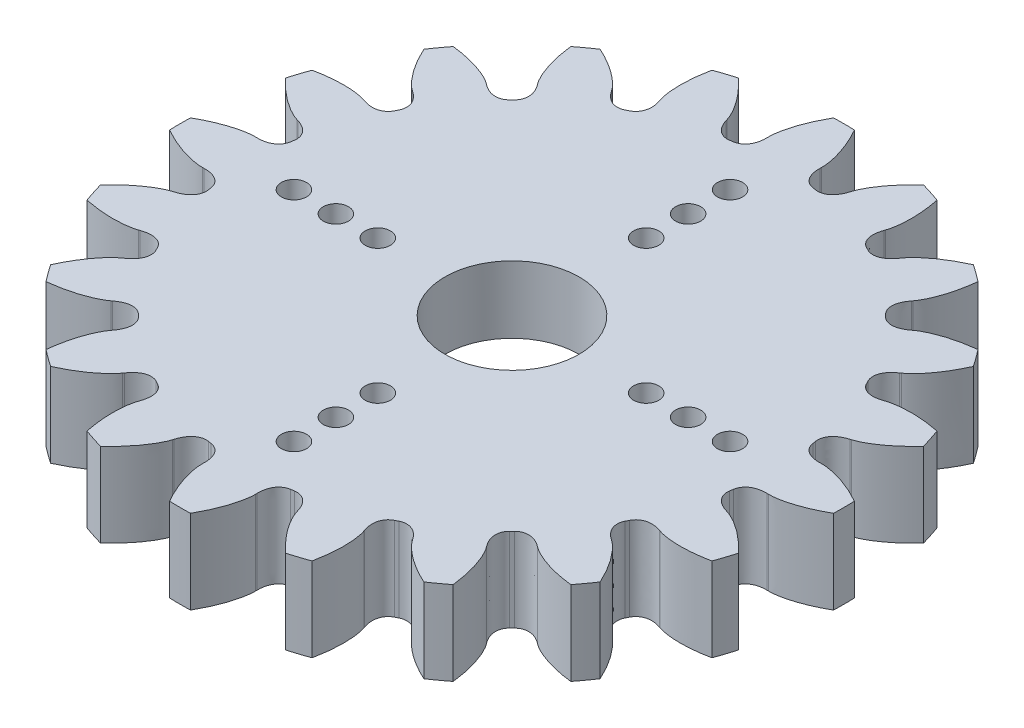
SolidWorks part; units mm, degrees
ref_plane "Front Plane" through (0, 0, 0) normal (0, 0, 1) x (1, 0, 0)
ref_plane "Top Plane" through (0, 0, 0) normal (0, 1, 0) x (1, 0, 0)
ref_plane "Right Plane" through (0, 0, 0) normal (1, 0, 0) x (0, 0, -1)
sketch "Sketch7" plane through (0, 0, 0) normal (0, 1, 0) x (1, 0, 0)
  line L80 (-16.4577, -3.6874) -> (-16.527, -3.709)
  line L81 (-16.8642, -1.5796) -> (-16.7917, -1.5788)
  line L82 (-16.7917, 1.5788) -> (-16.8642, 1.5796)
  line L83 (-16.527, 3.709) -> (-16.4577, 3.6874)
  line L84 (-15.482, 6.6904) -> (-15.5507, 6.7137)
  line L85 (-14.5719, 8.6346) -> (-14.5128, 8.5927)
  line L86 (-12.6568, 11.1472) -> (-12.715, 11.1905)
  line L87 (-11.1905, 12.715) -> (-11.1472, 12.6568)
  line L88 (-8.5927, 14.5128) -> (-8.6346, 14.5719)
  line L89 (-6.7137, 15.5507) -> (-6.6904, 15.482)
  line L90 (-3.6874, 16.4577) -> (-3.709, 16.527)
  line L91 (-1.5796, 16.8642) -> (-1.5788, 16.7917)
  line L92 (1.5788, 16.7917) -> (1.5796, 16.8642)
  line L93 (3.709, 16.527) -> (3.6874, 16.4577)
  line L94 (6.6904, 15.482) -> (6.7137, 15.5507)
  line L95 (8.6346, 14.5719) -> (8.5927, 14.5128)
  line L96 (11.1472, 12.6568) -> (11.1905, 12.715)
  line L97 (12.715, 11.1905) -> (12.6568, 11.1472)
  line L98 (14.5128, 8.5927) -> (14.5719, 8.6346)
  line L99 (15.5507, 6.7137) -> (15.482, 6.6904)
  line L100 (16.4577, 3.6874) -> (16.527, 3.709)
  line L101 (16.8642, 1.5796) -> (16.7917, 1.5788)
  line L102 (16.7917, -1.5788) -> (16.8642, -1.5796)
  line L103 (16.527, -3.709) -> (16.4577, -3.6874)
  line L104 (15.482, -6.6904) -> (15.5507, -6.7137)
  line L105 (14.5719, -8.6346) -> (14.5128, -8.5927)
  line L106 (12.6568, -11.1472) -> (12.715, -11.1905)
  line L107 (11.1905, -12.715) -> (11.1472, -12.6568)
  line L108 (8.5927, -14.5128) -> (8.6346, -14.5719)
  line L109 (6.7137, -15.5507) -> (6.6904, -15.482)
  line L110 (3.6874, -16.4577) -> (3.709, -16.527)
  line L111 (1.5796, -16.8642) -> (1.5788, -16.7917)
  line L112 (-1.5788, -16.7917) -> (-1.5796, -16.8642)
  line L113 (-3.709, -16.527) -> (-3.6874, -16.4577)
  line L114 (-6.6904, -15.482) -> (-6.7137, -15.5507)
  line L115 (-8.6346, -14.5719) -> (-8.5927, -14.5128)
  line L116 (-11.1472, -12.6568) -> (-11.1905, -12.715)
  line L117 (-12.715, -11.1905) -> (-12.6568, -11.1472)
  line L118 (-14.5128, -8.5927) -> (-14.5719, -8.6346)
  line L119 (-15.5507, -6.7137) -> (-15.482, -6.6904)
  arc A80 (-19.0148, -5.5208) -> (-18.6283, -6.7102) centre (0, 0) ccw
  arc A81 (-15.5716, -2.3637) -> (-15.5399, -2.5639) centre (0, 0) ccw
  arc A82 (-19.7901, 0.6253) -> (-19.7901, -0.6253) centre (0, 0) ccw
  arc A83 (-15.5399, 2.5639) -> (-15.5716, 2.3637) centre (0, 0) ccw
  arc A84 (-18.6283, 6.7102) -> (-19.0148, 5.5208) centre (0, 0) ccw
  arc A85 (-13.987, 7.2405) -> (-14.0791, 7.0599) centre (0, 0) ccw
  arc A86 (-15.643, 12.1382) -> (-16.3781, 11.1265) centre (0, 0) ccw
  arc A87 (-11.065, 11.2084) -> (-11.2084, 11.065) centre (0, 0) ccw
  arc A88 (-11.1265, 16.3781) -> (-12.1382, 15.643) centre (0, 0) ccw
  arc A89 (-7.0599, 14.0791) -> (-7.2405, 13.987) centre (0, 0) ccw
  arc A90 (-5.5208, 19.0148) -> (-6.7102, 18.6283) centre (0, 0) ccw
  arc A91 (-2.3637, 15.5716) -> (-2.5639, 15.5399) centre (0, 0) ccw
  arc A92 (0.6253, 19.7901) -> (-0.6253, 19.7901) centre (0, 0) ccw
  arc A93 (2.5639, 15.5399) -> (2.3637, 15.5716) centre (0, 0) ccw
  arc A94 (6.7102, 18.6283) -> (5.5208, 19.0148) centre (0, 0) ccw
  arc A95 (7.2405, 13.987) -> (7.0599, 14.0791) centre (0, 0) ccw
  arc A96 (12.1382, 15.643) -> (11.1265, 16.3781) centre (0, 0) ccw
  arc A97 (11.2084, 11.065) -> (11.065, 11.2084) centre (0, 0) ccw
  arc A98 (16.3781, 11.1265) -> (15.643, 12.1382) centre (0, 0) ccw
  arc A99 (14.0791, 7.0599) -> (13.987, 7.2405) centre (0, 0) ccw
  arc A100 (19.0148, 5.5208) -> (18.6283, 6.7102) centre (0, 0) ccw
  arc A101 (15.5716, 2.3637) -> (15.5399, 2.5639) centre (0, 0) ccw
  arc A102 (19.7901, -0.6253) -> (19.7901, 0.6253) centre (0, 0) ccw
  arc A103 (15.5399, -2.5639) -> (15.5716, -2.3637) centre (0, 0) ccw
  arc A104 (18.6283, -6.7102) -> (19.0148, -5.5208) centre (0, 0) ccw
  arc A105 (13.987, -7.2405) -> (14.0791, -7.0599) centre (0, 0) ccw
  arc A106 (15.643, -12.1382) -> (16.3781, -11.1265) centre (0, 0) ccw
  arc A107 (11.065, -11.2084) -> (11.2084, -11.065) centre (0, 0) ccw
  arc A108 (11.1265, -16.3781) -> (12.1382, -15.643) centre (0, 0) ccw
  arc A109 (7.0599, -14.0791) -> (7.2405, -13.987) centre (0, 0) ccw
  arc A110 (5.5208, -19.0148) -> (6.7102, -18.6283) centre (0, 0) ccw
  arc A111 (2.3637, -15.5716) -> (2.5639, -15.5399) centre (0, 0) ccw
  arc A112 (-0.6253, -19.7901) -> (0.6253, -19.7901) centre (0, 0) ccw
  arc A113 (-2.5639, -15.5399) -> (-2.3637, -15.5716) centre (0, 0) ccw
  arc A114 (-6.7102, -18.6283) -> (-5.5208, -19.0148) centre (0, 0) ccw
  arc A115 (-7.2405, -13.987) -> (-7.0599, -14.0791) centre (0, 0) ccw
  arc A116 (-12.1382, -15.643) -> (-11.1265, -16.3781) centre (0, 0) ccw
  arc A117 (-11.2084, -11.065) -> (-11.065, -11.2084) centre (0, 0) ccw
  arc A118 (-16.3781, -11.1265) -> (-15.643, -12.1382) centre (0, 0) ccw
  arc A119 (-14.0791, -7.0599) -> (-13.987, -7.2405) centre (0, 0) ccw
  spline S160 degree 3 poles (-16.527, -3.709) (-16.6119, -3.7336) (-16.7702, -3.7944) (-17.0187, -3.9123) (-17.2955, -4.0665) (-17.6234, -4.2783) (-17.9959, -4.555) (-18.4056, -4.9033) (-18.7477, -5.2353) (-18.9515, -5.4518) (-19.0148, -5.5208) knots 0 0 0 0 0.062091 0.118994 0.193136 0.284517 0.393136 0.518994 0.662091 0.72786 0.72786 0.72786 0.72786
  spline S161 degree 3 poles (-15.5399, -2.5639) (-15.5144, -2.7139) (-15.5425, -2.9348) (-15.672, -3.1736) (-15.7793, -3.3046) (-15.8929, -3.4073) (-16.0101, -3.4901) (-16.1313, -3.559) (-16.2793, -3.6275) (-16.3894, -3.6679) (-16.4577, -3.6874) knots 0 0 0 0 0.285204 0.404285 0.508742 0.603331 0.692375 0.779135 0.865928 1 1 1 1
  spline S162 degree 3 poles (-16.7917, -1.5788) (-16.7207, -1.5762) (-16.6035, -1.5807) (-16.4415, -1.6) (-16.305, -1.6281) (-16.1679, -1.6707) (-16.0282, -1.7332) (-15.8857, -1.8247) (-15.6887, -2.0117) (-15.5937, -2.2131) (-15.5716, -2.3637) knots 0 0 0 0 0.134072 0.220865 0.307625 0.396669 0.491258 0.595715 0.714796 1 1 1 1
  spline S163 degree 3 poles (-19.7901, -0.6253) (-19.7087, -0.6714) (-19.4479, -0.8143) (-19.02, -1.0243) (-18.5227, -1.2289) (-18.0829, -1.3771) (-17.7056, -1.4771) (-17.3947, -1.5383) (-17.122, -1.5736) (-16.9526, -1.5825) (-16.8642, -1.5796) knots 0.27214 0.27214 0.27214 0.27214 0.337909 0.481006 0.606864 0.715483 0.806864 0.881006 0.937909 1 1 1 1
  spline S164 degree 3 poles (-16.8642, 1.5796) (-16.9526, 1.5825) (-17.122, 1.5736) (-17.3947, 1.5383) (-17.7056, 1.4771) (-18.0829, 1.3771) (-18.5227, 1.2289) (-19.02, 1.0243) (-19.4479, 0.8143) (-19.7087, 0.6714) (-19.7901, 0.6253) knots 0 0 0 0 0.062091 0.118994 0.193136 0.284517 0.393136 0.518994 0.662091 0.72786 0.72786 0.72786 0.72786
  spline S165 degree 3 poles (-15.5716, 2.3637) (-15.5937, 2.2131) (-15.6887, 2.0117) (-15.8857, 1.8247) (-16.0282, 1.7332) (-16.1679, 1.6707) (-16.305, 1.6281) (-16.4415, 1.6) (-16.6035, 1.5807) (-16.7207, 1.5762) (-16.7917, 1.5788) knots 0 0 0 0 0.285204 0.404285 0.508742 0.603331 0.692375 0.779135 0.865928 1 1 1 1
  spline S166 degree 3 poles (-16.4577, 3.6874) (-16.3894, 3.6679) (-16.2793, 3.6275) (-16.1313, 3.559) (-16.0101, 3.4901) (-15.8929, 3.4073) (-15.7793, 3.3046) (-15.672, 3.1736) (-15.5425, 2.9348) (-15.5144, 2.7139) (-15.5399, 2.5639) knots 0 0 0 0 0.134072 0.220865 0.307625 0.396669 0.491258 0.595715 0.714796 1 1 1 1
  spline S167 degree 3 poles (-19.0148, 5.5208) (-18.9515, 5.4518) (-18.7477, 5.2353) (-18.4056, 4.9033) (-17.9959, 4.555) (-17.6234, 4.2783) (-17.2955, 4.0665) (-17.0187, 3.9123) (-16.7702, 3.7944) (-16.6119, 3.7336) (-16.527, 3.709) knots 0.27214 0.27214 0.27214 0.27214 0.337909 0.481006 0.606864 0.715483 0.806864 0.881006 0.937909 1 1 1 1
  spline S168 degree 3 poles (-15.5507, 6.7137) (-15.6339, 6.7437) (-15.7977, 6.7875) (-16.068, 6.8383) (-16.3825, 6.8762) (-16.7723, 6.8976) (-17.2364, 6.8926) (-17.7725, 6.8517) (-18.2445, 6.7842) (-18.5366, 6.7289) (-18.6283, 6.7102) knots 0 0 0 0 0.062091 0.118994 0.193136 0.284517 0.393136 0.518994 0.662091 0.72786 0.72786 0.72786 0.72786
  spline S169 degree 3 poles (-14.0791, 7.0599) (-14.1466, 6.9235) (-14.2992, 6.7613) (-14.5443, 6.6443) (-14.7081, 6.6014) (-14.8604, 6.5851) (-15.0039, 6.587) (-15.1424, 6.6024) (-15.3024, 6.6341) (-15.4152, 6.6661) (-15.482, 6.6904) knots 0 0 0 0 0.285204 0.404285 0.508742 0.603331 0.692375 0.779135 0.865928 1 1 1 1
  spline S170 degree 3 poles (-14.5128, 8.5927) (-14.4538, 8.553) (-14.3616, 8.4805) (-14.2419, 8.3697) (-14.148, 8.2667) (-14.0621, 8.1517) (-13.9858, 8.0189) (-13.9243, 7.8611) (-13.8749, 7.5941) (-13.9164, 7.3753) (-13.987, 7.2405) knots 0 0 0 0 0.134072 0.220865 0.307625 0.396669 0.491258 0.595715 0.714796 1 1 1 1
  spline S171 degree 3 poles (-16.3781, 11.1265) (-16.3393, 11.0413) (-16.2123, 10.7724) (-15.9896, 10.351) (-15.7076, 9.8931) (-15.4388, 9.5148) (-15.1923, 9.212) (-14.9768, 8.9799) (-14.7769, 8.791) (-14.6451, 8.6843) (-14.5719, 8.6346) knots 0.27214 0.27214 0.27214 0.27214 0.337909 0.481006 0.606864 0.715483 0.806864 0.881006 0.937909 1 1 1 1
  spline S172 degree 3 poles (-12.715, 11.1905) (-12.7848, 11.2447) (-12.9271, 11.3371) (-13.1685, 11.4689) (-13.4559, 11.6021) (-13.82, 11.7429) (-14.2628, 11.8816) (-14.7854, 12.0083) (-15.2551, 12.09) (-15.55, 12.1276) (-15.643, 12.1382) knots 0 0 0 0 0.062091 0.118994 0.193136 0.284517 0.393136 0.518994 0.662091 0.72786 0.72786 0.72786 0.72786
  spline S173 degree 3 poles (-11.2084, 11.065) (-11.3147, 10.9562) (-11.51, 10.8491) (-11.7792, 10.8136) (-11.9483, 10.8233) (-12.0981, 10.8549) (-12.2341, 10.901) (-12.361, 10.9585) (-12.5034, 11.0381) (-12.6008, 11.1034) (-12.6568, 11.1472) knots 0 0 0 0 0.285204 0.404285 0.508742 0.603331 0.692375 0.779135 0.865928 1 1 1 1
  spline S174 degree 3 poles (-11.1472, 12.6568) (-11.1034, 12.6008) (-11.0381, 12.5034) (-10.9585, 12.361) (-10.901, 12.2341) (-10.8549, 12.0981) (-10.8233, 11.9483) (-10.8136, 11.7792) (-10.8491, 11.51) (-10.9562, 11.3147) (-11.065, 11.2084) knots 0 0 0 0 0.134072 0.220865 0.307625 0.396669 0.491258 0.595715 0.714796 1 1 1 1
  spline S175 degree 3 poles (-12.1382, 15.643) (-12.1276, 15.55) (-12.09, 15.2551) (-12.0083, 14.7854) (-11.8816, 14.2628) (-11.7429, 13.82) (-11.6021, 13.4559) (-11.4689, 13.1685) (-11.3371, 12.9271) (-11.2447, 12.7848) (-11.1905, 12.715) knots 0.27214 0.27214 0.27214 0.27214 0.337909 0.481006 0.606864 0.715483 0.806864 0.881006 0.937909 1 1 1 1
  spline S176 degree 3 poles (-8.6346, 14.5719) (-8.6843, 14.6451) (-8.791, 14.7769) (-8.9799, 14.9768) (-9.212, 15.1923) (-9.5148, 15.4388) (-9.8931, 15.7076) (-10.351, 15.9896) (-10.7724, 16.2123) (-11.0413, 16.3393) (-11.1265, 16.3781) knots 0 0 0 0 0.062091 0.118994 0.193136 0.284517 0.393136 0.518994 0.662091 0.72786 0.72786 0.72786 0.72786
  spline S177 degree 3 poles (-7.2405, 13.987) (-7.3753, 13.9164) (-7.5941, 13.8749) (-7.8611, 13.9243) (-8.0189, 13.9858) (-8.1517, 14.0621) (-8.2667, 14.148) (-8.3697, 14.2419) (-8.4805, 14.3616) (-8.553, 14.4538) (-8.5927, 14.5128) knots 0 0 0 0 0.285204 0.404285 0.508742 0.603331 0.692375 0.779135 0.865928 1 1 1 1
  spline S178 degree 3 poles (-6.6904, 15.482) (-6.6661, 15.4152) (-6.6341, 15.3024) (-6.6024, 15.1424) (-6.587, 15.0039) (-6.5851, 14.8604) (-6.6014, 14.7081) (-6.6443, 14.5443) (-6.7613, 14.2992) (-6.9235, 14.1466) (-7.0599, 14.0791) knots 0 0 0 0 0.134072 0.220865 0.307625 0.396669 0.491258 0.595715 0.714796 1 1 1 1
  spline S179 degree 3 poles (-6.7102, 18.6283) (-6.7289, 18.5366) (-6.7842, 18.2445) (-6.8517, 17.7725) (-6.8926, 17.2364) (-6.8976, 16.7723) (-6.8762, 16.3825) (-6.8383, 16.068) (-6.7875, 15.7977) (-6.7437, 15.6339) (-6.7137, 15.5507) knots 0.27214 0.27214 0.27214 0.27214 0.337909 0.481006 0.606864 0.715483 0.806864 0.881006 0.937909 1 1 1 1
  spline S180 degree 3 poles (-3.709, 16.527) (-3.7336, 16.6119) (-3.7944, 16.7702) (-3.9123, 17.0187) (-4.0665, 17.2955) (-4.2783, 17.6234) (-4.555, 17.9959) (-4.9033, 18.4056) (-5.2353, 18.7477) (-5.4518, 18.9515) (-5.5208, 19.0148) knots 0 0 0 0 0.062091 0.118994 0.193136 0.284517 0.393136 0.518994 0.662091 0.72786 0.72786 0.72786 0.72786
  spline S181 degree 3 poles (-2.5639, 15.5399) (-2.7139, 15.5144) (-2.9348, 15.5425) (-3.1736, 15.672) (-3.3046, 15.7793) (-3.4073, 15.8929) (-3.4901, 16.0101) (-3.559, 16.1313) (-3.6275, 16.2793) (-3.6679, 16.3894) (-3.6874, 16.4577) knots 0 0 0 0 0.285204 0.404285 0.508742 0.603331 0.692375 0.779135 0.865928 1 1 1 1
  spline S182 degree 3 poles (-1.5788, 16.7917) (-1.5762, 16.7207) (-1.5807, 16.6035) (-1.6, 16.4415) (-1.6281, 16.305) (-1.6707, 16.1679) (-1.7332, 16.0282) (-1.8247, 15.8857) (-2.0117, 15.6887) (-2.2131, 15.5937) (-2.3637, 15.5716) knots 0 0 0 0 0.134072 0.220865 0.307625 0.396669 0.491258 0.595715 0.714796 1 1 1 1
  spline S183 degree 3 poles (-0.6253, 19.7901) (-0.6714, 19.7087) (-0.8143, 19.4479) (-1.0243, 19.02) (-1.2289, 18.5227) (-1.3771, 18.0829) (-1.4771, 17.7056) (-1.5383, 17.3947) (-1.5736, 17.122) (-1.5825, 16.9526) (-1.5796, 16.8642) knots 0.27214 0.27214 0.27214 0.27214 0.337909 0.481006 0.606864 0.715483 0.806864 0.881006 0.937909 1 1 1 1
  spline S184 degree 3 poles (1.5796, 16.8642) (1.5825, 16.9526) (1.5736, 17.122) (1.5383, 17.3947) (1.4771, 17.7056) (1.3771, 18.0829) (1.2289, 18.5227) (1.0243, 19.02) (0.8143, 19.4479) (0.6714, 19.7087) (0.6253, 19.7901) knots 0 0 0 0 0.062091 0.118994 0.193136 0.284517 0.393136 0.518994 0.662091 0.72786 0.72786 0.72786 0.72786
  spline S185 degree 3 poles (2.3637, 15.5716) (2.2131, 15.5937) (2.0117, 15.6887) (1.8247, 15.8857) (1.7332, 16.0282) (1.6707, 16.1679) (1.6281, 16.305) (1.6, 16.4415) (1.5807, 16.6035) (1.5762, 16.7207) (1.5788, 16.7917) knots 0 0 0 0 0.285204 0.404285 0.508742 0.603331 0.692375 0.779135 0.865928 1 1 1 1
  spline S186 degree 3 poles (3.6874, 16.4577) (3.6679, 16.3894) (3.6275, 16.2793) (3.559, 16.1313) (3.4901, 16.0101) (3.4073, 15.8929) (3.3046, 15.7793) (3.1736, 15.672) (2.9348, 15.5425) (2.7139, 15.5144) (2.5639, 15.5399) knots 0 0 0 0 0.134072 0.220865 0.307625 0.396669 0.491258 0.595715 0.714796 1 1 1 1
  spline S187 degree 3 poles (5.5208, 19.0148) (5.4518, 18.9515) (5.2353, 18.7477) (4.9033, 18.4056) (4.555, 17.9959) (4.2783, 17.6234) (4.0665, 17.2955) (3.9123, 17.0187) (3.7944, 16.7702) (3.7336, 16.6119) (3.709, 16.527) knots 0.27214 0.27214 0.27214 0.27214 0.337909 0.481006 0.606864 0.715483 0.806864 0.881006 0.937909 1 1 1 1
  spline S188 degree 3 poles (6.7137, 15.5507) (6.7437, 15.6339) (6.7875, 15.7977) (6.8383, 16.068) (6.8762, 16.3825) (6.8976, 16.7723) (6.8926, 17.2364) (6.8517, 17.7725) (6.7842, 18.2445) (6.7289, 18.5366) (6.7102, 18.6283) knots 0 0 0 0 0.062091 0.118994 0.193136 0.284517 0.393136 0.518994 0.662091 0.72786 0.72786 0.72786 0.72786
  spline S189 degree 3 poles (7.0599, 14.0791) (6.9235, 14.1466) (6.7613, 14.2992) (6.6443, 14.5443) (6.6014, 14.7081) (6.5851, 14.8604) (6.587, 15.0039) (6.6024, 15.1424) (6.6341, 15.3024) (6.6661, 15.4152) (6.6904, 15.482) knots 0 0 0 0 0.285204 0.404285 0.508742 0.603331 0.692375 0.779135 0.865928 1 1 1 1
  spline S190 degree 3 poles (8.5927, 14.5128) (8.553, 14.4538) (8.4805, 14.3616) (8.3697, 14.2419) (8.2667, 14.148) (8.1517, 14.0621) (8.0189, 13.9858) (7.8611, 13.9243) (7.5941, 13.8749) (7.3753, 13.9164) (7.2405, 13.987) knots 0 0 0 0 0.134072 0.220865 0.307625 0.396669 0.491258 0.595715 0.714796 1 1 1 1
  spline S191 degree 3 poles (11.1265, 16.3781) (11.0413, 16.3393) (10.7724, 16.2123) (10.351, 15.9896) (9.8931, 15.7076) (9.5148, 15.4388) (9.212, 15.1923) (8.9799, 14.9768) (8.791, 14.7769) (8.6843, 14.6451) (8.6346, 14.5719) knots 0.27214 0.27214 0.27214 0.27214 0.337909 0.481006 0.606864 0.715483 0.806864 0.881006 0.937909 1 1 1 1
  spline S192 degree 3 poles (11.1905, 12.715) (11.2447, 12.7848) (11.3371, 12.9271) (11.4689, 13.1685) (11.6021, 13.4559) (11.7429, 13.82) (11.8816, 14.2628) (12.0083, 14.7854) (12.09, 15.2551) (12.1276, 15.55) (12.1382, 15.643) knots 0 0 0 0 0.062091 0.118994 0.193136 0.284517 0.393136 0.518994 0.662091 0.72786 0.72786 0.72786 0.72786
  spline S193 degree 3 poles (11.065, 11.2084) (10.9562, 11.3147) (10.8491, 11.51) (10.8136, 11.7792) (10.8233, 11.9483) (10.8549, 12.0981) (10.901, 12.2341) (10.9585, 12.361) (11.0381, 12.5034) (11.1034, 12.6008) (11.1472, 12.6568) knots 0 0 0 0 0.285204 0.404285 0.508742 0.603331 0.692375 0.779135 0.865928 1 1 1 1
  spline S194 degree 3 poles (12.6568, 11.1472) (12.6008, 11.1034) (12.5034, 11.0381) (12.361, 10.9585) (12.2341, 10.901) (12.0981, 10.8549) (11.9483, 10.8233) (11.7792, 10.8136) (11.51, 10.8491) (11.3147, 10.9562) (11.2084, 11.065) knots 0 0 0 0 0.134072 0.220865 0.307625 0.396669 0.491258 0.595715 0.714796 1 1 1 1
  spline S195 degree 3 poles (15.643, 12.1382) (15.55, 12.1276) (15.2551, 12.09) (14.7854, 12.0083) (14.2628, 11.8816) (13.82, 11.7429) (13.4559, 11.6021) (13.1685, 11.4689) (12.9271, 11.3371) (12.7848, 11.2447) (12.715, 11.1905) knots 0.27214 0.27214 0.27214 0.27214 0.337909 0.481006 0.606864 0.715483 0.806864 0.881006 0.937909 1 1 1 1
  spline S196 degree 3 poles (14.5719, 8.6346) (14.6451, 8.6843) (14.7769, 8.791) (14.9768, 8.9799) (15.1923, 9.212) (15.4388, 9.5148) (15.7076, 9.8931) (15.9896, 10.351) (16.2123, 10.7724) (16.3393, 11.0413) (16.3781, 11.1265) knots 0 0 0 0 0.062091 0.118994 0.193136 0.284517 0.393136 0.518994 0.662091 0.72786 0.72786 0.72786 0.72786
  spline S197 degree 3 poles (13.987, 7.2405) (13.9164, 7.3753) (13.8749, 7.5941) (13.9243, 7.8611) (13.9858, 8.0189) (14.0621, 8.1517) (14.148, 8.2667) (14.2419, 8.3697) (14.3616, 8.4805) (14.4538, 8.553) (14.5128, 8.5927) knots 0 0 0 0 0.285204 0.404285 0.508742 0.603331 0.692375 0.779135 0.865928 1 1 1 1
  spline S198 degree 3 poles (15.482, 6.6904) (15.4152, 6.6661) (15.3024, 6.6341) (15.1424, 6.6024) (15.0039, 6.587) (14.8604, 6.5851) (14.7081, 6.6014) (14.5443, 6.6443) (14.2992, 6.7613) (14.1466, 6.9235) (14.0791, 7.0599) knots 0 0 0 0 0.134072 0.220865 0.307625 0.396669 0.491258 0.595715 0.714796 1 1 1 1
  spline S199 degree 3 poles (18.6283, 6.7102) (18.5366, 6.7289) (18.2445, 6.7842) (17.7725, 6.8517) (17.2364, 6.8926) (16.7723, 6.8976) (16.3825, 6.8762) (16.068, 6.8383) (15.7977, 6.7875) (15.6339, 6.7437) (15.5507, 6.7137) knots 0.27214 0.27214 0.27214 0.27214 0.337909 0.481006 0.606864 0.715483 0.806864 0.881006 0.937909 1 1 1 1
  spline S200 degree 3 poles (16.527, 3.709) (16.6119, 3.7336) (16.7702, 3.7944) (17.0187, 3.9123) (17.2955, 4.0665) (17.6234, 4.2783) (17.9959, 4.555) (18.4056, 4.9033) (18.7477, 5.2353) (18.9515, 5.4518) (19.0148, 5.5208) knots 0 0 0 0 0.062091 0.118994 0.193136 0.284517 0.393136 0.518994 0.662091 0.72786 0.72786 0.72786 0.72786
  spline S201 degree 3 poles (15.5399, 2.5639) (15.5144, 2.7139) (15.5425, 2.9348) (15.672, 3.1736) (15.7793, 3.3046) (15.8929, 3.4073) (16.0101, 3.4901) (16.1313, 3.559) (16.2793, 3.6275) (16.3894, 3.6679) (16.4577, 3.6874) knots 0 0 0 0 0.285204 0.404285 0.508742 0.603331 0.692375 0.779135 0.865928 1 1 1 1
  spline S202 degree 3 poles (16.7917, 1.5788) (16.7207, 1.5762) (16.6035, 1.5807) (16.4415, 1.6) (16.305, 1.6281) (16.1679, 1.6707) (16.0282, 1.7332) (15.8857, 1.8247) (15.6887, 2.0117) (15.5937, 2.2131) (15.5716, 2.3637) knots 0 0 0 0 0.134072 0.220865 0.307625 0.396669 0.491258 0.595715 0.714796 1 1 1 1
  spline S203 degree 3 poles (19.7901, 0.6253) (19.7087, 0.6714) (19.4479, 0.8143) (19.02, 1.0243) (18.5227, 1.2289) (18.0829, 1.3771) (17.7056, 1.4771) (17.3947, 1.5383) (17.122, 1.5736) (16.9526, 1.5825) (16.8642, 1.5796) knots 0.27214 0.27214 0.27214 0.27214 0.337909 0.481006 0.606864 0.715483 0.806864 0.881006 0.937909 1 1 1 1
  spline S204 degree 3 poles (16.8642, -1.5796) (16.9526, -1.5825) (17.122, -1.5736) (17.3947, -1.5383) (17.7056, -1.4771) (18.0829, -1.3771) (18.5227, -1.2289) (19.02, -1.0243) (19.4479, -0.8143) (19.7087, -0.6714) (19.7901, -0.6253) knots 0 0 0 0 0.062091 0.118994 0.193136 0.284517 0.393136 0.518994 0.662091 0.72786 0.72786 0.72786 0.72786
  spline S205 degree 3 poles (15.5716, -2.3637) (15.5937, -2.2131) (15.6887, -2.0117) (15.8857, -1.8247) (16.0282, -1.7332) (16.1679, -1.6707) (16.305, -1.6281) (16.4415, -1.6) (16.6035, -1.5807) (16.7207, -1.5762) (16.7917, -1.5788) knots 0 0 0 0 0.285204 0.404285 0.508742 0.603331 0.692375 0.779135 0.865928 1 1 1 1
  spline S206 degree 3 poles (16.4577, -3.6874) (16.3894, -3.6679) (16.2793, -3.6275) (16.1313, -3.559) (16.0101, -3.4901) (15.8929, -3.4073) (15.7793, -3.3046) (15.672, -3.1736) (15.5425, -2.9348) (15.5144, -2.7139) (15.5399, -2.5639) knots 0 0 0 0 0.134072 0.220865 0.307625 0.396669 0.491258 0.595715 0.714796 1 1 1 1
  spline S207 degree 3 poles (19.0148, -5.5208) (18.9515, -5.4518) (18.7477, -5.2353) (18.4056, -4.9033) (17.9959, -4.555) (17.6234, -4.2783) (17.2955, -4.0665) (17.0187, -3.9123) (16.7702, -3.7944) (16.6119, -3.7336) (16.527, -3.709) knots 0.27214 0.27214 0.27214 0.27214 0.337909 0.481006 0.606864 0.715483 0.806864 0.881006 0.937909 1 1 1 1
  spline S208 degree 3 poles (15.5507, -6.7137) (15.6339, -6.7437) (15.7977, -6.7875) (16.068, -6.8383) (16.3825, -6.8762) (16.7723, -6.8976) (17.2364, -6.8926) (17.7725, -6.8517) (18.2445, -6.7842) (18.5366, -6.7289) (18.6283, -6.7102) knots 0 0 0 0 0.062091 0.118994 0.193136 0.284517 0.393136 0.518994 0.662091 0.72786 0.72786 0.72786 0.72786
  spline S209 degree 3 poles (14.0791, -7.0599) (14.1466, -6.9235) (14.2992, -6.7613) (14.5443, -6.6443) (14.7081, -6.6014) (14.8604, -6.5851) (15.0039, -6.587) (15.1424, -6.6024) (15.3024, -6.6341) (15.4152, -6.6661) (15.482, -6.6904) knots 0 0 0 0 0.285204 0.404285 0.508742 0.603331 0.692375 0.779135 0.865928 1 1 1 1
  spline S210 degree 3 poles (14.5128, -8.5927) (14.4538, -8.553) (14.3616, -8.4805) (14.2419, -8.3697) (14.148, -8.2667) (14.0621, -8.1517) (13.9858, -8.0189) (13.9243, -7.8611) (13.8749, -7.5941) (13.9164, -7.3753) (13.987, -7.2405) knots 0 0 0 0 0.134072 0.220865 0.307625 0.396669 0.491258 0.595715 0.714796 1 1 1 1
  spline S211 degree 3 poles (16.3781, -11.1265) (16.3393, -11.0413) (16.2123, -10.7724) (15.9896, -10.351) (15.7076, -9.8931) (15.4388, -9.5148) (15.1923, -9.212) (14.9768, -8.9799) (14.7769, -8.791) (14.6451, -8.6843) (14.5719, -8.6346) knots 0.27214 0.27214 0.27214 0.27214 0.337909 0.481006 0.606864 0.715483 0.806864 0.881006 0.937909 1 1 1 1
  spline S212 degree 3 poles (12.715, -11.1905) (12.7848, -11.2447) (12.9271, -11.3371) (13.1685, -11.4689) (13.4559, -11.6021) (13.82, -11.7429) (14.2628, -11.8816) (14.7854, -12.0083) (15.2551, -12.09) (15.55, -12.1276) (15.643, -12.1382) knots 0 0 0 0 0.062091 0.118994 0.193136 0.284517 0.393136 0.518994 0.662091 0.72786 0.72786 0.72786 0.72786
  spline S213 degree 3 poles (11.2084, -11.065) (11.3147, -10.9562) (11.51, -10.8491) (11.7792, -10.8136) (11.9483, -10.8233) (12.0981, -10.8549) (12.2341, -10.901) (12.361, -10.9585) (12.5034, -11.0381) (12.6008, -11.1034) (12.6568, -11.1472) knots 0 0 0 0 0.285204 0.404285 0.508742 0.603331 0.692375 0.779135 0.865928 1 1 1 1
  spline S214 degree 3 poles (11.1472, -12.6568) (11.1034, -12.6008) (11.0381, -12.5034) (10.9585, -12.361) (10.901, -12.2341) (10.8549, -12.0981) (10.8233, -11.9483) (10.8136, -11.7792) (10.8491, -11.51) (10.9562, -11.3147) (11.065, -11.2084) knots 0 0 0 0 0.134072 0.220865 0.307625 0.396669 0.491258 0.595715 0.714796 1 1 1 1
  spline S215 degree 3 poles (12.1382, -15.643) (12.1276, -15.55) (12.09, -15.2551) (12.0083, -14.7854) (11.8816, -14.2628) (11.7429, -13.82) (11.6021, -13.4559) (11.4689, -13.1685) (11.3371, -12.9271) (11.2447, -12.7848) (11.1905, -12.715) knots 0.27214 0.27214 0.27214 0.27214 0.337909 0.481006 0.606864 0.715483 0.806864 0.881006 0.937909 1 1 1 1
  spline S216 degree 3 poles (8.6346, -14.5719) (8.6843, -14.6451) (8.791, -14.7769) (8.9799, -14.9768) (9.212, -15.1923) (9.5148, -15.4388) (9.8931, -15.7076) (10.351, -15.9896) (10.7724, -16.2123) (11.0413, -16.3393) (11.1265, -16.3781) knots 0 0 0 0 0.062091 0.118994 0.193136 0.284517 0.393136 0.518994 0.662091 0.72786 0.72786 0.72786 0.72786
  spline S217 degree 3 poles (7.2405, -13.987) (7.3753, -13.9164) (7.5941, -13.8749) (7.8611, -13.9243) (8.0189, -13.9858) (8.1517, -14.0621) (8.2667, -14.148) (8.3697, -14.2419) (8.4805, -14.3616) (8.553, -14.4538) (8.5927, -14.5128) knots 0 0 0 0 0.285204 0.404285 0.508742 0.603331 0.692375 0.779135 0.865928 1 1 1 1
  spline S218 degree 3 poles (6.6904, -15.482) (6.6661, -15.4152) (6.6341, -15.3024) (6.6024, -15.1424) (6.587, -15.0039) (6.5851, -14.8604) (6.6014, -14.7081) (6.6443, -14.5443) (6.7613, -14.2992) (6.9235, -14.1466) (7.0599, -14.0791) knots 0 0 0 0 0.134072 0.220865 0.307625 0.396669 0.491258 0.595715 0.714796 1 1 1 1
  spline S219 degree 3 poles (6.7102, -18.6283) (6.7289, -18.5366) (6.7842, -18.2445) (6.8517, -17.7725) (6.8926, -17.2364) (6.8976, -16.7723) (6.8762, -16.3825) (6.8383, -16.068) (6.7875, -15.7977) (6.7437, -15.6339) (6.7137, -15.5507) knots 0.27214 0.27214 0.27214 0.27214 0.337909 0.481006 0.606864 0.715483 0.806864 0.881006 0.937909 1 1 1 1
  spline S220 degree 3 poles (3.709, -16.527) (3.7336, -16.6119) (3.7944, -16.7702) (3.9123, -17.0187) (4.0665, -17.2955) (4.2783, -17.6234) (4.555, -17.9959) (4.9033, -18.4056) (5.2353, -18.7477) (5.4518, -18.9515) (5.5208, -19.0148) knots 0 0 0 0 0.062091 0.118994 0.193136 0.284517 0.393136 0.518994 0.662091 0.72786 0.72786 0.72786 0.72786
  spline S221 degree 3 poles (2.5639, -15.5399) (2.7139, -15.5144) (2.9348, -15.5425) (3.1736, -15.672) (3.3046, -15.7793) (3.4073, -15.8929) (3.4901, -16.0101) (3.559, -16.1313) (3.6275, -16.2793) (3.6679, -16.3894) (3.6874, -16.4577) knots 0 0 0 0 0.285204 0.404285 0.508742 0.603331 0.692375 0.779135 0.865928 1 1 1 1
  spline S222 degree 3 poles (1.5788, -16.7917) (1.5762, -16.7207) (1.5807, -16.6035) (1.6, -16.4415) (1.6281, -16.305) (1.6707, -16.1679) (1.7332, -16.0282) (1.8247, -15.8857) (2.0117, -15.6887) (2.2131, -15.5937) (2.3637, -15.5716) knots 0 0 0 0 0.134072 0.220865 0.307625 0.396669 0.491258 0.595715 0.714796 1 1 1 1
  spline S223 degree 3 poles (0.6253, -19.7901) (0.6714, -19.7087) (0.8143, -19.4479) (1.0243, -19.02) (1.2289, -18.5227) (1.3771, -18.0829) (1.4771, -17.7056) (1.5383, -17.3947) (1.5736, -17.122) (1.5825, -16.9526) (1.5796, -16.8642) knots 0.27214 0.27214 0.27214 0.27214 0.337909 0.481006 0.606864 0.715483 0.806864 0.881006 0.937909 1 1 1 1
  spline S224 degree 3 poles (-1.5796, -16.8642) (-1.5825, -16.9526) (-1.5736, -17.122) (-1.5383, -17.3947) (-1.4771, -17.7056) (-1.3771, -18.0829) (-1.2289, -18.5227) (-1.0243, -19.02) (-0.8143, -19.4479) (-0.6714, -19.7087) (-0.6253, -19.7901) knots 0 0 0 0 0.062091 0.118994 0.193136 0.284517 0.393136 0.518994 0.662091 0.72786 0.72786 0.72786 0.72786
  spline S225 degree 3 poles (-2.3637, -15.5716) (-2.2131, -15.5937) (-2.0117, -15.6887) (-1.8247, -15.8857) (-1.7332, -16.0282) (-1.6707, -16.1679) (-1.6281, -16.305) (-1.6, -16.4415) (-1.5807, -16.6035) (-1.5762, -16.7207) (-1.5788, -16.7917) knots 0 0 0 0 0.285204 0.404285 0.508742 0.603331 0.692375 0.779135 0.865928 1 1 1 1
  spline S226 degree 3 poles (-3.6874, -16.4577) (-3.6679, -16.3894) (-3.6275, -16.2793) (-3.559, -16.1313) (-3.4901, -16.0101) (-3.4073, -15.8929) (-3.3046, -15.7793) (-3.1736, -15.672) (-2.9348, -15.5425) (-2.7139, -15.5144) (-2.5639, -15.5399) knots 0 0 0 0 0.134072 0.220865 0.307625 0.396669 0.491258 0.595715 0.714796 1 1 1 1
  spline S227 degree 3 poles (-5.5208, -19.0148) (-5.4518, -18.9515) (-5.2353, -18.7477) (-4.9033, -18.4056) (-4.555, -17.9959) (-4.2783, -17.6234) (-4.0665, -17.2955) (-3.9123, -17.0187) (-3.7944, -16.7702) (-3.7336, -16.6119) (-3.709, -16.527) knots 0.27214 0.27214 0.27214 0.27214 0.337909 0.481006 0.606864 0.715483 0.806864 0.881006 0.937909 1 1 1 1
  spline S228 degree 3 poles (-6.7137, -15.5507) (-6.7437, -15.6339) (-6.7875, -15.7977) (-6.8383, -16.068) (-6.8762, -16.3825) (-6.8976, -16.7723) (-6.8926, -17.2364) (-6.8517, -17.7725) (-6.7842, -18.2445) (-6.7289, -18.5366) (-6.7102, -18.6283) knots 0 0 0 0 0.062091 0.118994 0.193136 0.284517 0.393136 0.518994 0.662091 0.72786 0.72786 0.72786 0.72786
  spline S229 degree 3 poles (-7.0599, -14.0791) (-6.9235, -14.1466) (-6.7613, -14.2992) (-6.6443, -14.5443) (-6.6014, -14.7081) (-6.5851, -14.8604) (-6.587, -15.0039) (-6.6024, -15.1424) (-6.6341, -15.3024) (-6.6661, -15.4152) (-6.6904, -15.482) knots 0 0 0 0 0.285204 0.404285 0.508742 0.603331 0.692375 0.779135 0.865928 1 1 1 1
  spline S230 degree 3 poles (-8.5927, -14.5128) (-8.553, -14.4538) (-8.4805, -14.3616) (-8.3697, -14.2419) (-8.2667, -14.148) (-8.1517, -14.0621) (-8.0189, -13.9858) (-7.8611, -13.9243) (-7.5941, -13.8749) (-7.3753, -13.9164) (-7.2405, -13.987) knots 0 0 0 0 0.134072 0.220865 0.307625 0.396669 0.491258 0.595715 0.714796 1 1 1 1
  spline S231 degree 3 poles (-11.1265, -16.3781) (-11.0413, -16.3393) (-10.7724, -16.2123) (-10.351, -15.9896) (-9.8931, -15.7076) (-9.5148, -15.4388) (-9.212, -15.1923) (-8.9799, -14.9768) (-8.791, -14.7769) (-8.6843, -14.6451) (-8.6346, -14.5719) knots 0.27214 0.27214 0.27214 0.27214 0.337909 0.481006 0.606864 0.715483 0.806864 0.881006 0.937909 1 1 1 1
  spline S232 degree 3 poles (-11.1905, -12.715) (-11.2447, -12.7848) (-11.3371, -12.9271) (-11.4689, -13.1685) (-11.6021, -13.4559) (-11.7429, -13.82) (-11.8816, -14.2628) (-12.0083, -14.7854) (-12.09, -15.2551) (-12.1276, -15.55) (-12.1382, -15.643) knots 0 0 0 0 0.062091 0.118994 0.193136 0.284517 0.393136 0.518994 0.662091 0.72786 0.72786 0.72786 0.72786
  spline S233 degree 3 poles (-11.065, -11.2084) (-10.9562, -11.3147) (-10.8491, -11.51) (-10.8136, -11.7792) (-10.8233, -11.9483) (-10.8549, -12.0981) (-10.901, -12.2341) (-10.9585, -12.361) (-11.0381, -12.5034) (-11.1034, -12.6008) (-11.1472, -12.6568) knots 0 0 0 0 0.285204 0.404285 0.508742 0.603331 0.692375 0.779135 0.865928 1 1 1 1
  spline S234 degree 3 poles (-12.6568, -11.1472) (-12.6008, -11.1034) (-12.5034, -11.0381) (-12.361, -10.9585) (-12.2341, -10.901) (-12.0981, -10.8549) (-11.9483, -10.8233) (-11.7792, -10.8136) (-11.51, -10.8491) (-11.3147, -10.9562) (-11.2084, -11.065) knots 0 0 0 0 0.134072 0.220865 0.307625 0.396669 0.491258 0.595715 0.714796 1 1 1 1
  spline S235 degree 3 poles (-15.643, -12.1382) (-15.55, -12.1276) (-15.2551, -12.09) (-14.7854, -12.0083) (-14.2628, -11.8816) (-13.82, -11.7429) (-13.4559, -11.6021) (-13.1685, -11.4689) (-12.9271, -11.3371) (-12.7848, -11.2447) (-12.715, -11.1905) knots 0.27214 0.27214 0.27214 0.27214 0.337909 0.481006 0.606864 0.715483 0.806864 0.881006 0.937909 1 1 1 1
  spline S236 degree 3 poles (-14.5719, -8.6346) (-14.6451, -8.6843) (-14.7769, -8.791) (-14.9768, -8.9799) (-15.1923, -9.212) (-15.4388, -9.5148) (-15.7076, -9.8931) (-15.9896, -10.351) (-16.2123, -10.7724) (-16.3393, -11.0413) (-16.3781, -11.1265) knots 0 0 0 0 0.062091 0.118994 0.193136 0.284517 0.393136 0.518994 0.662091 0.72786 0.72786 0.72786 0.72786
  spline S237 degree 3 poles (-13.987, -7.2405) (-13.9164, -7.3753) (-13.8749, -7.5941) (-13.9243, -7.8611) (-13.9858, -8.0189) (-14.0621, -8.1517) (-14.148, -8.2667) (-14.2419, -8.3697) (-14.3616, -8.4805) (-14.4538, -8.553) (-14.5128, -8.5927) knots 0 0 0 0 0.285204 0.404285 0.508742 0.603331 0.692375 0.779135 0.865928 1 1 1 1
  spline S238 degree 3 poles (-15.482, -6.6904) (-15.4152, -6.6661) (-15.3024, -6.6341) (-15.1424, -6.6024) (-15.0039, -6.587) (-14.8604, -6.5851) (-14.7081, -6.6014) (-14.5443, -6.6443) (-14.2992, -6.7613) (-14.1466, -6.9235) (-14.0791, -7.0599) knots 0 0 0 0 0.134072 0.220865 0.307625 0.396669 0.491258 0.595715 0.714796 1 1 1 1
  spline S239 degree 3 poles (-18.6283, -6.7102) (-18.5366, -6.7289) (-18.2445, -6.7842) (-17.7725, -6.8517) (-17.2364, -6.8926) (-16.7723, -6.8976) (-16.3825, -6.8762) (-16.068, -6.8383) (-15.7977, -6.7875) (-15.6339, -6.7437) (-15.5507, -6.7137) knots 0.27214 0.27214 0.27214 0.27214 0.337909 0.481006 0.606864 0.715483 0.806864 0.881006 0.937909 1 1 1 1
extrude "Boss-Extrude1" add sketch "Sketch7" along normal blind 5
sketch "Sketch8" plane through (0, 0, 0) normal (0, -1, 0) x (1, 0, 0)
  line L0 (-2.5, -15.5) -> (-4.5, -4.5)
  line L1 (-4.5, -4.5) -> (-15.5, -2.5)
  line L2 (-15.5, 2.5) -> (-4.5, 4.5)
  line L3 (-4.5, 4.5) -> (-2.5, 15.5)
  line L4 (2.5, 15.5) -> (4.5, 4.5)
  line L5 (4.5, 4.5) -> (-4.5, -4.5) construction
  line L6 (4.5, -4.5) -> (-4.5, 4.5) construction
  line L7 (-2.5, -15.5) -> (2.5, -15.5)
  line L8 (4.5, 4.5) -> (15.5, 2.5)
  line L9 (-2.5, 15.5) -> (2.5, 15.5)
  line L10 (15.5, -2.5) -> (4.5, -4.5)
  line L11 (-2.5, -15.5) -> (2.5, 15.5) construction
  line L12 (-2.5, 15.5) -> (2.5, -15.5) construction
  line L13 (4.5, -4.5) -> (2.5, -15.5)
  line L14 (15.5, 2.5) -> (15.5, -2.5)
  line L16 (-15.5, 2.5) -> (-15.5, -2.5)
  line L17 (15.5, 2.5) -> (-15.5, -2.5) construction
  line L18 (15.5, -2.5) -> (-15.5, 2.5) construction
  point P0 (0, 0)
  point P5 (0, 0)
  point P6 (0, 0)
  point P12 (0, 0)
  point P17 (0, 0)
  point P18 (0, 0)
  point P19 (0, 0)
  point P20 (0, 0)
  point P21 (15.5, 0)
  point P22 (-15.5, 0)
  point P23 (0, 0)
  point P24 (0, 15.5)
  point P25 (0, -15.5)
  point P26 (0, 0)
  point P27 (0, 0)
  point P28 (0, 0)
  point P29 (0, 0)
  point P30 (0, 0)
  point P31 (0, 0)
  dimension "D1" = 5
  dimension "D2" = 5
  dimension "D3" = 9
  dimension "D4" = 9
extrude "Cut-Extrude2" cut sketch "Sketch8" against normal blind 1 contours L3 L9 L4 L8 L14 L10 L13 L7 L0 L1 L16 L2
fillet "Fillet1" radius 2 12 edges at (2.5, 0.5, 15.5) (4.5, 0.5, 4.5) (15.5, 0.5, 2.5) (15.5, 0.5, -2.5) (4.5, 0.5, -4.5) (2.5, 0.5, -15.5) (-2.5, 0.5, -15.5) (-4.5, 0.5, -4.5) (-15.5, 0.5, -2.5) (-15.5, 0.5, 2.5) (-4.5, 0.5, 4.5) (-2.5, 0.5, 15.5)
sketch "Sketch10" plane through (0, 0, 0) normal (0, -1, 0) x (1, 0, 0)
  circle A0 centre (8, 0) radius 0.75
  circle A1 centre (10.5, 0) radius 0.75
  circle A2 centre (13, 0) radius 0.75
  circle A3 centre (0, 0) radius 4
  circle A4 centre (0, -8) radius 0.75
  circle A5 centre (0, -10.5) radius 0.75
  circle A6 centre (0, -13) radius 0.75
  circle A7 centre (-8, 0) radius 0.75
  circle A8 centre (-10.5, 0) radius 0.75
  circle A9 centre (-13, 0) radius 0.75
  circle A10 centre (0, 8) radius 0.75
  circle A11 centre (0, 10.5) radius 0.75
  circle A12 centre (0, 13) radius 0.75
  point P30 (0, 0)
  dimension "D4" = 4
  dimension "D2" = 1.5
  dimension "D3" = 1.5
  dimension "D5" = 1.5
  dimension "D6" = 6.7901
  dimension "D7" = 9.2901
  dimension "D8" = 11.7901
  dimension "D11" = 8
extrude "Cut-Extrude3" cut sketch "Sketch10" against normal through all
